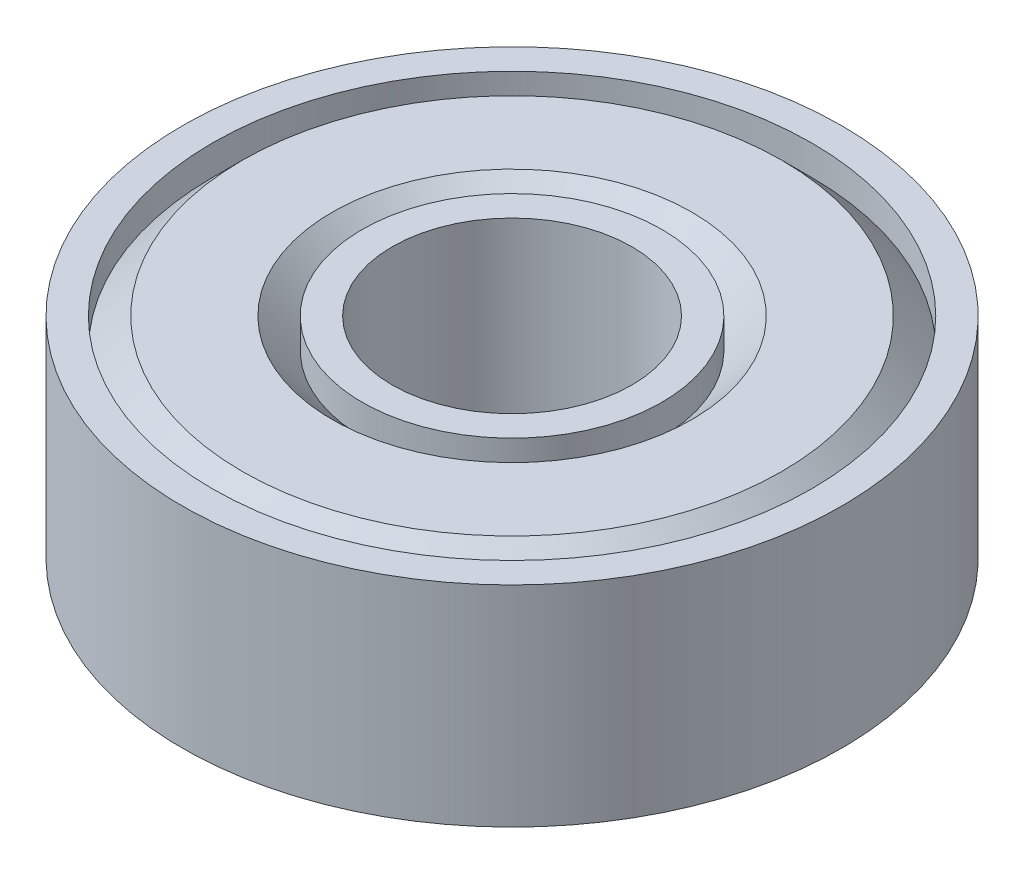
SolidWorks part; units mm, degrees
ref_plane "前视基准面" through (0, 0, 0) normal (0, 0, 1) x (1, 0, 0)
ref_plane "上视基准面" through (0, 0, 0) normal (0, 1, 0) x (1, 0, 0)
ref_plane "右视基准面" through (0, 0, 0) normal (1, 0, 0) x (0, 0, -1)
sketch "草图1" plane through (0, 0, 0) normal (0, 0, 1) x (1, 0, 0)
  line L0 (-20, 0) -> (-19, 0)
  line L1 (-19, 0) -> (-19, 7)
  line L2 (-19, 7) -> (-20, 7)
  line L3 (-20, 7) -> (-20, 6)
  line L4 (-20, 6) -> (-21, 7)
  line L5 (-21, 7) -> (-24, 7)
  line L6 (-24, 7) -> (-25, 6)
  line L7 (-25, 6) -> (-25, 7)
  line L8 (-25, 7) -> (-26, 7)
  line L9 (-26, 7) -> (-26, 0)
  line L10 (-26, 0) -> (-25, 0)
  line L11 (-25, 0) -> (-25, 1)
  line L12 (-25, 1) -> (-24, 0)
  line L13 (-24, 0) -> (-21, 0)
  line L14 (-21, 0) -> (-20, 1)
  line L15 (-20, 1) -> (-20, 0)
  line L16 (-30, 7) -> (-30, 0) construction
revolve "旋转1" add sketch "草图1" angle 360 about L16
